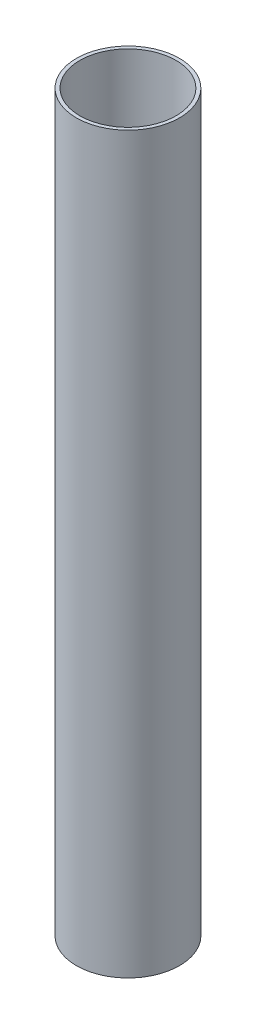
SolidWorks part; units mm, degrees
ref_plane "Front Plane" through (0, 0, 0) normal (0, 0, 1) x (1, 0, 0)
ref_plane "Top Plane" through (0, 0, 0) normal (0, 1, 0) x (1, 0, 0)
ref_plane "Right Plane" through (0, 0, 0) normal (1, 0, 0) x (0, 0, -1)
sketch "Sketch1" plane through (0, 0, 0) normal (0, 1, 0) x (1, 0, 0)
  circle A0 centre (0, 0) radius 29.5
  circle A1 centre (0, 0) radius 27.5
  dimension "D1" = 55
  dimension "D2" = 59
extrude "Boss-Extrude1" add sketch "Sketch1" along normal blind 420
sketch "Sketch2" plane through (0, 420, 0) normal (0, 1, 0) x (1, 0, 0)
  line L0 (-65.3571, 18.4647) -> (-30, 43.0842)
  line L1 (30, 43.0842) -> (65.3571, 18.4647)
  line L2 (65.3571, -18.4647) -> (30, -43.0842)
  line L3 (-65.3571, -18.4647) -> (-30, -43.0842)
  arc A0 (-30, -43.0842) -> (30, -43.0842) centre (0, 0) ccw
  arc A1 (65.3571, -18.4647) -> (65.3571, 18.4647) centre (52.5, 0) ccw
  arc A2 (-65.3571, 18.4647) -> (-65.3571, -18.4647) centre (-52.5, 0) ccw
  arc A3 (30, 43.0842) -> (-30, 43.0842) centre (0, 0) ccw
  circle A8 centre (0, 0) radius 27.5 construction
  circle A9 centre (0, 0) radius 27.5
  dimension "D1" = 105
  dimension "D2" = 45
  dimension "D3" = 45
extrude "Boss-Extrude2" [suppressed] add sketch "Sketch2" along normal blind 5
sketch "Sketch3" [suppressed] plane through (0, 0, 0) normal (0, 0, 1) x (1, 0, 0)
  line L0 (-194.2145, 315) -> (49805.7855, 315) construction
  line L1 (30, 425) -> (-30, 425) construction
  line L2 (0, 0) -> (0, 50000) construction
  circle A0 centre (0, 315) radius 1.5
  circle A1 centre (0, 305) radius 1.5
  circle A2 centre (0, 295) radius 1.5
  dimension "D4" = 3
  dimension "D5" = 3
  dimension "D6" = 3
  dimension "D1" = 110
  dimension "D2" = 10
  dimension "D3" = 10
extrude "Cut-Extrude1" [suppressed] cut sketch "Sketch3" against normal through all both and the other way through all
sketch "Sketch4" [suppressed] plane through (0, 0, 0) normal (1, 0, 0) x (0, 0, -1)
  line L0 (0, 0) -> (0, 50000) construction
  line L1 (0, 315) -> (-50000, 315) construction
  line L2 (18.4647, 425) -> (-18.4647, 425) construction
  circle A0 centre (0, 305) radius 1.5
  circle A1 centre (0, 315) radius 1.5
  circle A2 centre (0, 295) radius 1.5
  dimension "D2" = 3
  dimension "D1" = 110
  dimension "D3" = 10
  dimension "D4" = 10
extrude "Cut-Extrude2" [suppressed] cut sketch "Sketch4" against normal through all both and the other way through all
ref_plane "Plane1" through (0, 0, 0) normal (-0.7071, 0, 0.7071) x (0, -1, 0)
ref_plane "Plane2" through (0, 0, 0) normal (-0.7071, 0, -0.7071) x (0, -1, 0)
pattern_linear "LPattern1" [suppressed] count 5 spacing 60 count 2 spacing 45
sketch "Sketch5" [suppressed] plane through (0, 0, 0) normal (-0.7071, 0, -0.7071) x (0, -1, 0)
  line L0 (-307, 0) -> (-307, 50000) construction
  line L2 (0, 0) -> (-50000, 0) construction
  line L4 (-425, -9.2519) -> (-425, 33.158) construction
  circle A0 centre (-307, 0) radius 1.5
  circle A1 centre (-297, 0) radius 1.5
  circle A2 centre (-287, 0) radius 1.5
  dimension "D4" = 3
  dimension "D1" = 118
  dimension "D2" = 10
  dimension "D3" = 10
extrude "Cut-Extrude3" [suppressed] cut sketch "Sketch5" against normal through all both and the other way through all
sketch "Sketch6" [suppressed] plane through (0, 0, 0) normal (-0.7071, 0, 0.7071) x (0, -1, 0)
  line L0 (-307, 0) -> (-307, 50000) construction
  line L2 (0, 0) -> (-50000, 0) construction
  line L4 (-425, -33.158) -> (-425, 9.2519) construction
  circle A0 centre (-307, 0) radius 1.5
  circle A1 centre (-297, 0) radius 1.5
  circle A2 centre (-287, 0) radius 1.5
  dimension "D2" = 3
  dimension "D1" = 118
  dimension "D3" = 3
extrude "Cut-Extrude4" [suppressed] cut sketch "Sketch6" against normal through all both and the other way through all
pattern_linear "LPattern2" [suppressed] count 5 spacing 60 count 2 spacing 45
